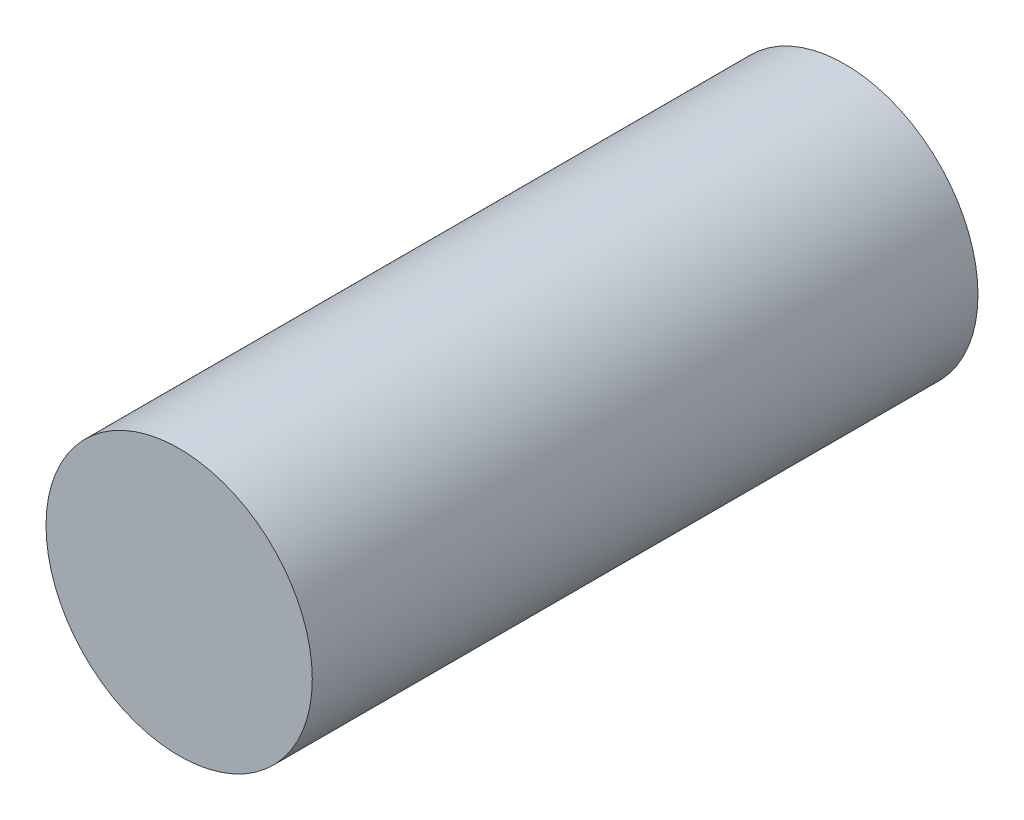
SolidWorks part; units mm, degrees
ref_plane "Front Plane" through (0, 0, 0) normal (0, 0, 1) x (1, 0, 0)
ref_plane "Top Plane" through (0, 0, 0) normal (0, 1, 0) x (1, 0, 0)
ref_plane "Right Plane" through (0, 0, 0) normal (1, 0, 0) x (0, 0, -1)
sketch "Sketch2" plane through (0, 0, 0) normal (0, 0, 1) x (1, 0, 0)
  circle A0 centre (0, 0) radius 20
  dimension "D1" = 40
extrude "Boss-Extrude1" add sketch "Sketch2" along normal blind 100
